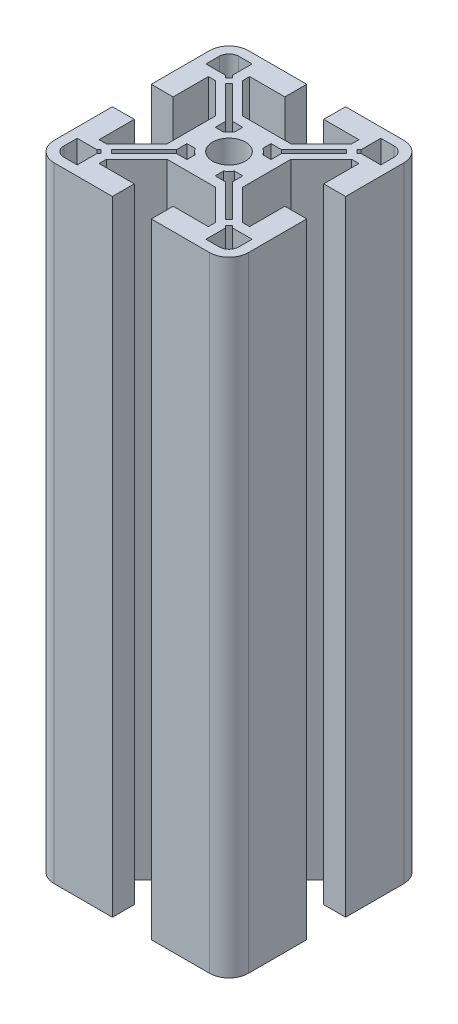
SolidWorks part; units mm, degrees
ref_plane "Ebene vorne" through (0, 0, 0) normal (0, 0, 1) x (1, 0, 0)
ref_plane "Ebene oben" through (0, 0, 0) normal (0, 1, 0) x (1, 0, 0)
ref_plane "Ebene rechts" through (0, 0, 0) normal (1, 0, 0) x (0, 0, -1)
sketch "Sketch1" plane through (0, 0, 0) normal (0, 1, 0) x (1, 0, 0)
  line L0 (-7.9326, -10.8599) -> (-58.869, -10.8599) construction
  line L1 (-7.9326, -10.8599) -> (-7.9326, 43.7859) construction
  line L2 (-7.9326, -10.8599) -> (-62.5783, 43.7859) construction
  line L3 (-27.9326, -6.8599) -> (-27.9326, 5.1401)
  line L4 (-27.9326, -6.8599) -> (-23.4326, -6.8599)
  line L5 (-23.4326, -6.8599) -> (-23.4326, 0.3901)
  line L6 (-23.4326, 0.3901) -> (-21.9326, 0.3901)
  line L7 (-21.9326, 0.3901) -> (-15.6826, -5.8599)
  line L8 (-15.6826, -5.8599) -> (-15.6826, -10.8599)
  line L9 (-25.9326, 2.3901) -> (-25.9326, 5.1401)
  line L10 (-25.9326, 2.3901) -> (-21.8897, 2.3901)
  line L11 (-21.4415, 1.9419) -> (-20.7344, 2.649)
  line L12 (-21.4415, 1.9419) -> (-21.8897, 2.3901)
  line L13 (-20.3808, 0.8813) -> (-13.6826, -5.817)
  line L14 (-13.6826, -5.817) -> (-13.6826, -7.9551)
  line L15 (-20.3808, 0.8813) -> (-19.6737, 1.5884)
  line L16 (-13.6826, -7.9551) -> (-13.1826, -7.9551)
  line L17 (-19.6737, 1.5884) -> (-12.9755, -5.1099)
  line L18 (-10.8374, -5.1099) -> (-10.8374, -5.6099)
  line L19 (-12.9755, -5.1099) -> (-10.8374, -5.1099)
  line L20 (-21.1826, 7.1401) -> (-21.1826, 3.0973)
  line L21 (-21.1826, 7.1401) -> (-23.9326, 7.1401)
  line L22 (-19.1826, 3.1401) -> (-12.9326, -3.1099)
  line L23 (-11.9326, 9.1401) -> (-11.9326, 4.6401)
  line L24 (-19.1826, 4.6401) -> (-19.1826, 3.1401)
  line L25 (-12.9326, -3.1099) -> (-7.9326, -3.1099)
  line L26 (-11.9326, 4.6401) -> (-19.1826, 4.6401)
  line L27 (-11.9326, 9.1401) -> (-23.9326, 9.1401)
  line L28 (7.5674, -6.8599) -> (7.5674, 0.3901)
  line L29 (12.0674, -6.8599) -> (12.0674, 5.1401)
  line L30 (12.0674, -6.8599) -> (7.5674, -6.8599)
  line L31 (10.0674, 2.3901) -> (10.0674, 5.1401)
  line L32 (10.0674, 2.3901) -> (6.0245, 2.3901)
  line L33 (6.0674, 0.3901) -> (-0.1826, -5.8599)
  line L34 (7.5674, 0.3901) -> (6.0674, 0.3901)
  line L35 (-0.1826, -5.8599) -> (-0.1826, -10.8599)
  line L36 (-2.1826, -5.817) -> (-2.1826, -7.9551)
  line L37 (3.8085, 1.5884) -> (-2.8897, -5.1099)
  line L38 (4.5156, 0.8813) -> (-2.1826, -5.817)
  line L39 (-2.8897, -5.1099) -> (-5.0279, -5.1099)
  line L40 (-5.0279, -5.1099) -> (-5.0279, -5.6099)
  line L41 (-2.1826, -7.9551) -> (-2.6826, -7.9551)
  line L42 (-2.9326, -3.1099) -> (-7.9326, -3.1099)
  line L43 (3.3174, 3.1401) -> (-2.9326, -3.1099)
  line L44 (5.3174, 7.1401) -> (5.3174, 3.0973)
  line L45 (5.3174, 7.1401) -> (8.0674, 7.1401)
  line L46 (-3.9326, 4.6401) -> (3.3174, 4.6401)
  line L47 (3.3174, 4.6401) -> (3.3174, 3.1401)
  line L48 (-3.9326, 9.1401) -> (8.0674, 9.1401)
  line L49 (-3.9326, 9.1401) -> (-3.9326, 4.6401)
  line L50 (-3.9326, -26.3599) -> (3.3174, -26.3599)
  line L51 (-3.9326, -30.8599) -> (8.0674, -30.8599)
  line L52 (-3.9326, -30.8599) -> (-3.9326, -26.3599)
  line L53 (5.3174, -28.8599) -> (8.0674, -28.8599)
  line L54 (5.3174, -28.8599) -> (5.3174, -24.817)
  line L55 (3.3174, -24.8599) -> (-2.9326, -18.6099)
  line L56 (3.3174, -26.3599) -> (3.3174, -24.8599)
  line L57 (-2.9326, -18.6099) -> (-7.9326, -18.6099)
  line L58 (-2.8897, -16.6099) -> (-5.0279, -16.6099)
  line L59 (4.5156, -22.601) -> (-2.1826, -15.9027)
  line L60 (3.8085, -23.3081) -> (-2.8897, -16.6099)
  line L61 (-2.1826, -15.9027) -> (-2.1826, -13.7646)
  line L62 (-2.1826, -13.7646) -> (-2.6826, -13.7646)
  line L63 (-5.0279, -16.6099) -> (-5.0279, -16.1099)
  line L64 (-0.1826, -15.8599) -> (-0.1826, -10.8599)
  line L65 (6.0674, -22.1099) -> (-0.1826, -15.8599)
  line L66 (10.0674, -24.1099) -> (6.0245, -24.1099)
  line L67 (10.0674, -24.1099) -> (10.0674, -26.8599)
  line L68 (7.5674, -14.8599) -> (7.5674, -22.1099)
  line L69 (7.5674, -22.1099) -> (6.0674, -22.1099)
  line L70 (12.0674, -14.8599) -> (12.0674, -26.8599)
  line L71 (12.0674, -14.8599) -> (7.5674, -14.8599)
  line L72 (-23.4326, -14.8599) -> (-23.4326, -22.1099)
  line L73 (-27.9326, -14.8599) -> (-27.9326, -26.8599)
  line L74 (-27.9326, -14.8599) -> (-23.4326, -14.8599)
  line L75 (-25.9326, -24.1099) -> (-25.9326, -26.8599)
  line L76 (-25.9326, -24.1099) -> (-21.8897, -24.1099)
  line L77 (-21.9326, -22.1099) -> (-15.6826, -15.8599)
  line L78 (-23.4326, -22.1099) -> (-21.9326, -22.1099)
  line L79 (-15.6826, -15.8599) -> (-15.6826, -10.8599)
  line L80 (-13.6826, -15.9027) -> (-13.6826, -13.7646)
  line L81 (-19.6737, -23.3081) -> (-12.9755, -16.6099)
  line L82 (-20.3808, -22.601) -> (-13.6826, -15.9027)
  line L83 (-12.9755, -16.6099) -> (-10.8374, -16.6099)
  line L84 (-10.8374, -16.6099) -> (-10.8374, -16.1099)
  line L85 (-13.6826, -13.7646) -> (-13.1826, -13.7646)
  line L86 (-12.9326, -18.6099) -> (-7.9326, -18.6099)
  line L87 (-19.1826, -24.8599) -> (-12.9326, -18.6099)
  line L88 (-21.1826, -28.8599) -> (-21.1826, -24.817)
  line L89 (-21.1826, -28.8599) -> (-23.9326, -28.8599)
  line L90 (-11.9326, -26.3599) -> (-19.1826, -26.3599)
  line L91 (-19.1826, -26.3599) -> (-19.1826, -24.8599)
  line L92 (-11.9326, -30.8599) -> (-23.9326, -30.8599)
  line L93 (-11.9326, -30.8599) -> (-11.9326, -26.3599)
  line L94 (-20.7344, 2.649) -> (-21.1826, 3.0973)
  line L95 (4.8692, 2.649) -> (5.3174, 3.0973)
  line L96 (4.8692, 2.649) -> (5.5763, 1.9419)
  line L97 (5.5763, 1.9419) -> (6.0245, 2.3901)
  line L98 (3.8085, 1.5884) -> (4.5156, 0.8813)
  line L99 (5.5763, -23.6616) -> (6.0245, -24.1099)
  line L100 (5.5763, -23.6616) -> (4.8692, -24.3687)
  line L101 (4.8692, -24.3687) -> (5.3174, -24.817)
  line L102 (4.5156, -22.601) -> (3.8085, -23.3081)
  line L103 (-20.7344, -24.3687) -> (-21.1826, -24.817)
  line L104 (-20.7344, -24.3687) -> (-21.4415, -23.6616)
  line L105 (-21.4415, -23.6616) -> (-21.8897, -24.1099)
  line L106 (-19.6737, -23.3081) -> (-20.3808, -22.601)
  line L107 (-13.1826, -7.9551) -> (-12.0023, -7.9551)
  line L108 (-10.8374, -5.6099) -> (-10.8374, -6.7901)
  line L109 (-5.0279, -5.6099) -> (-5.0279, -6.7901)
  line L110 (-2.6826, -7.9551) -> (-3.8629, -7.9551)
  line L111 (-2.6826, -13.7646) -> (-3.8629, -13.7646)
  line L112 (-5.0279, -16.1099) -> (-5.0279, -14.9296)
  line L113 (-10.8374, -16.1099) -> (-10.8374, -14.9296)
  line L114 (-13.1826, -13.7646) -> (-12.0023, -13.7646)
  arc A0 (-27.9326, 5.1401) -> (-23.9326, 9.1401) centre (-23.9326, 5.1401) cw
  arc A1 (-25.9326, 5.1401) -> (-23.9326, 7.1401) centre (-23.9326, 5.1401) cw
  arc A2 (-11.3326, -10.8599) -> (-7.9326, -7.4599) centre (-7.9326, -10.8599) cw
  arc A3 (-12.0023, -13.7646) -> (-10.8374, -14.9296) centre (-7.9326, -10.8599) ccw
  arc A4 (8.0674, 9.1401) -> (12.0674, 5.1401) centre (8.0674, 5.1401) cw
  arc A5 (8.0674, 7.1401) -> (10.0674, 5.1401) centre (8.0674, 5.1401) cw
  arc A6 (-5.0279, -14.9296) -> (-3.8629, -13.7646) centre (-7.9326, -10.8599) ccw
  arc A7 (-7.9326, -7.4599) -> (-4.5326, -10.8599) centre (-7.9326, -10.8599) cw
  arc A8 (12.0674, -26.8599) -> (8.0674, -30.8599) centre (8.0674, -26.8599) cw
  arc A9 (10.0674, -26.8599) -> (8.0674, -28.8599) centre (8.0674, -26.8599) cw
  arc A10 (-3.8629, -7.9551) -> (-5.0279, -6.7901) centre (-7.9326, -10.8599) ccw
  arc A11 (-4.5326, -10.8599) -> (-7.9326, -14.2599) centre (-7.9326, -10.8599) cw
  arc A12 (-23.9326, -30.8599) -> (-27.9326, -26.8599) centre (-23.9326, -26.8599) cw
  arc A13 (-23.9326, -28.8599) -> (-25.9326, -26.8599) centre (-23.9326, -26.8599) cw
  arc A14 (-10.8374, -6.7901) -> (-12.0023, -7.9551) centre (-7.9326, -10.8599) ccw
  arc A15 (-7.9326, -14.2599) -> (-11.3326, -10.8599) centre (-7.9326, -10.8599) cw
  point P19 (-20.0273, 1.2348)
  point P41 (-21.0879, 2.2955)
  point P140 (-7.9326, -10.8599)
  point P149 (-7.9326, -10.8599)
  point P152 (-7.9326, -10.8599)
extrude "Boss-Extrude1" add sketch "Sketch1" along normal mid plane 128.5 contours A12 L92 L93 L90 L91 L87 L86 L57 L55 L56 L50 L52 L51 A8 L70 L71 L68 L69 L65 L64 L35 L33 L34 L28 L30 L29 A4 L48 L49 L46 L47 L43 L42 L25 L22 L24 L26 L23 L27 A0 L3 L4 L5 L6 L7 L8 L79 L77 L78 L72 L74
